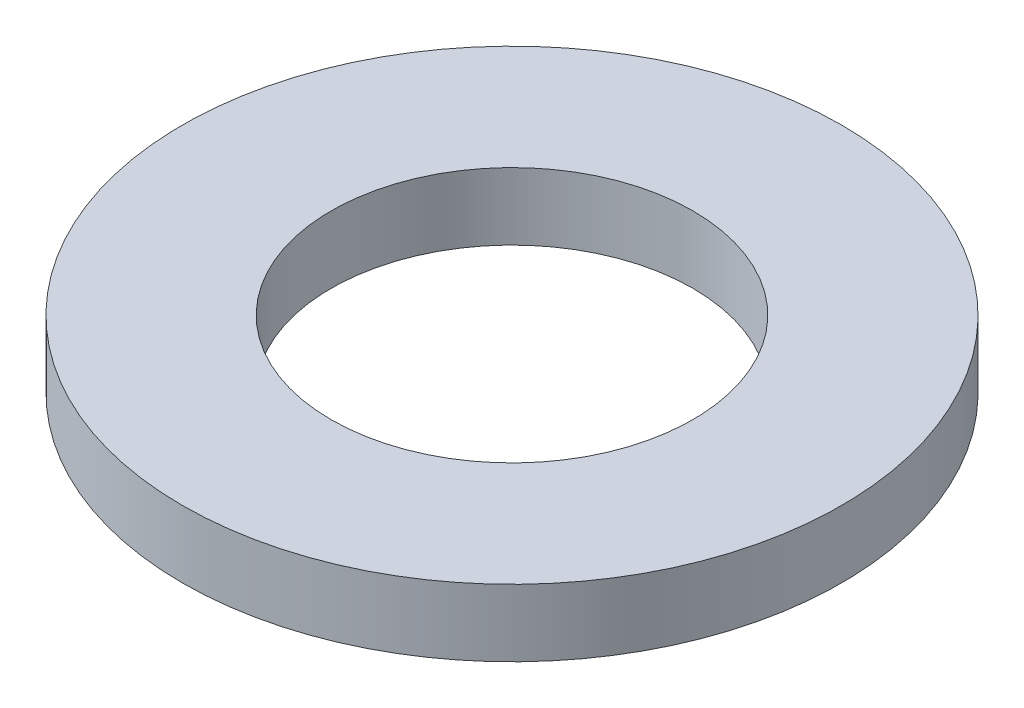
SolidWorks part; units mm, degrees
material "Plain Carbon Steel"
ref_plane "Front Plane" through (0, 0, 0) normal (0, 0, 1) x (1, 0, 0)
ref_plane "Top Plane" through (0, 0, 0) normal (0, 1, 0) x (1, 0, 0)
ref_plane "Right Plane" through (0, 0, 0) normal (1, 0, 0) x (0, 0, -1)
sketch "Sketch1" plane through (0, 0, 0) normal (0, 1, 0) x (1, 0, 0)
  circle A0 centre (0, 0) radius 4.91
  circle A1 centre (0, 0) radius 2.695
  dimension "D1" = 9.82
  dimension "D2" = 5.39
extrude "Boss-Extrude1" add sketch "Sketch1" along normal mid plane 1
